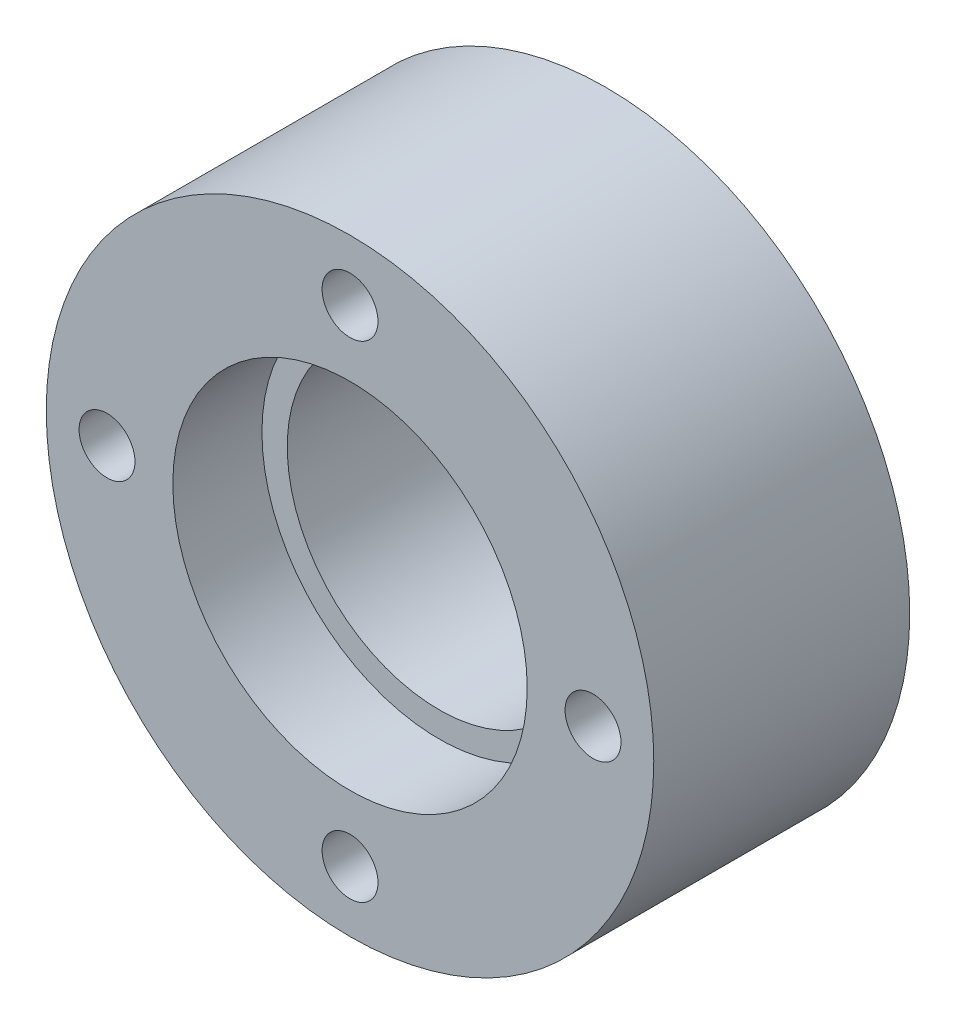
SolidWorks part; units mm, degrees
ref_plane "Front Plane" through (0, 0, 0) normal (0, 0, 1) x (1, 0, 0)
ref_plane "Top Plane" through (0, 0, 0) normal (0, 1, 0) x (1, 0, 0)
ref_plane "Right Plane" through (0, 0, 0) normal (1, 0, 0) x (0, 0, -1)
sketch "Sketch1" plane through (0, 0, 0) normal (0, 0, 1) x (1, 0, 0)
  circle A0 centre (0, 0) radius 19.05
  circle A1 centre (0, 0) radius 9.525
  circle A2 centre (0, 15.24) radius 1.7526
  circle A3 centre (15.24, 0) radius 1.7526
  circle A4 centre (0, -15.24) radius 1.7526
  circle A5 centre (-15.24, 0) radius 1.7526
  point P7 (13.727, 6.6201)
  point P16 (0, 0)
  dimension "D1" = 19.05
  dimension "D2" = 3.5052
  dimension "D5" = 38.1
  dimension "D4" = 15.24
  dimension "D3" = 4
extrude "Boss-Extrude1" add sketch "Sketch1" along normal blind 16.0528
sketch "Sketch2" plane through (0, 0, 16.0528) normal (0, 0, 1) x (1, 0, 0)
  circle A0 centre (0, 0) radius 11.1125
  dimension "D1" = 22.225
extrude "Cut-Extrude2" cut sketch "Sketch2" against normal blind 5.588
